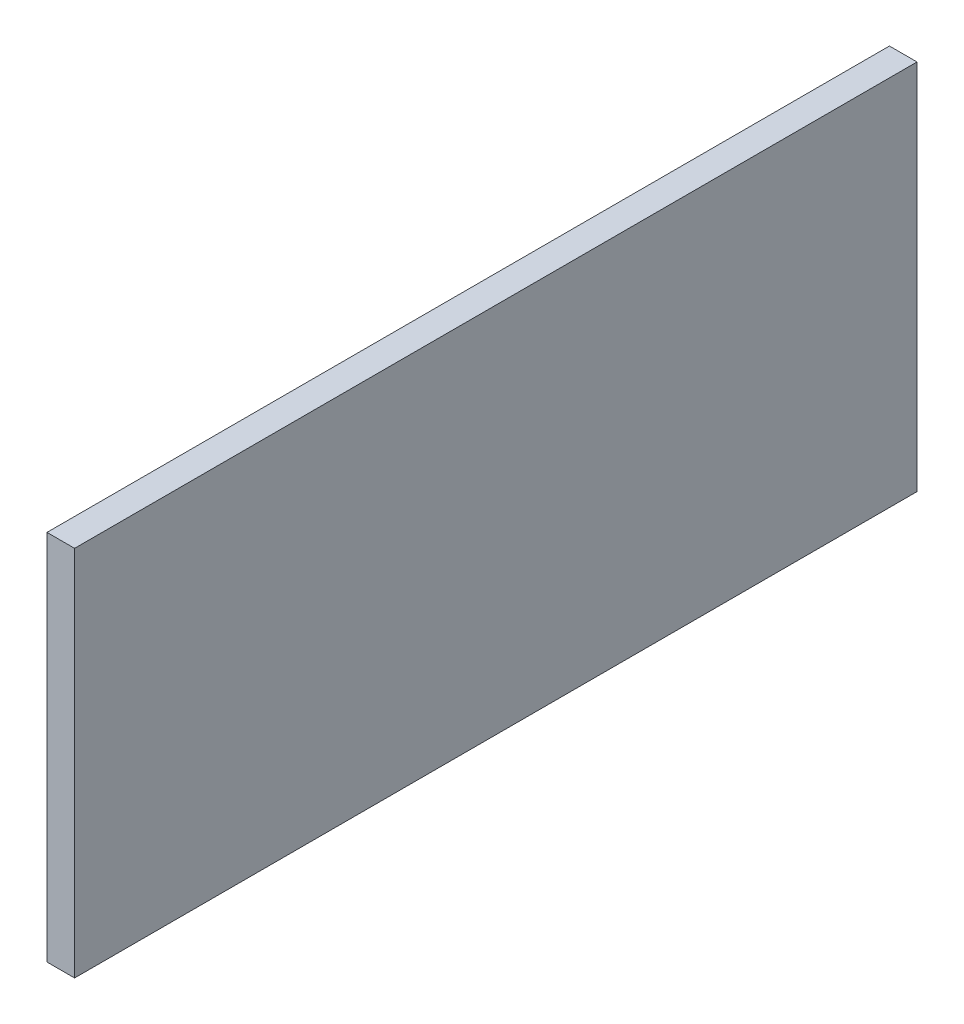
SolidWorks part; units mm, degrees
ref_plane "Plan de face" through (0, 0, 0) normal (0, 0, 1) x (1, 0, 0)
ref_plane "Plan de dessus" through (0, 0, 0) normal (0, 1, 0) x (1, 0, 0)
ref_plane "Plan de droite" through (0, 0, 0) normal (1, 0, 0) x (0, 0, -1)
sketch "Esquisse1" plane through (0, 0, 0) normal (0, 0, 1) x (1, 0, 0)
  line L1 (-167.4148, -20.1861) -> (-152.1648, -20.1861)
  line L2 (-167.4148, -20.1861) -> (-167.4148, 185.3139)
  line L3 (-167.4148, 185.3139) -> (-152.1648, 185.3139)
  line L4 (-152.1648, -20.1861) -> (-152.1648, 185.3139)
  dimension "D1" = 15.25
extrude "Boss.-Extru.1" add sketch "Esquisse1" along normal blind 465.25
